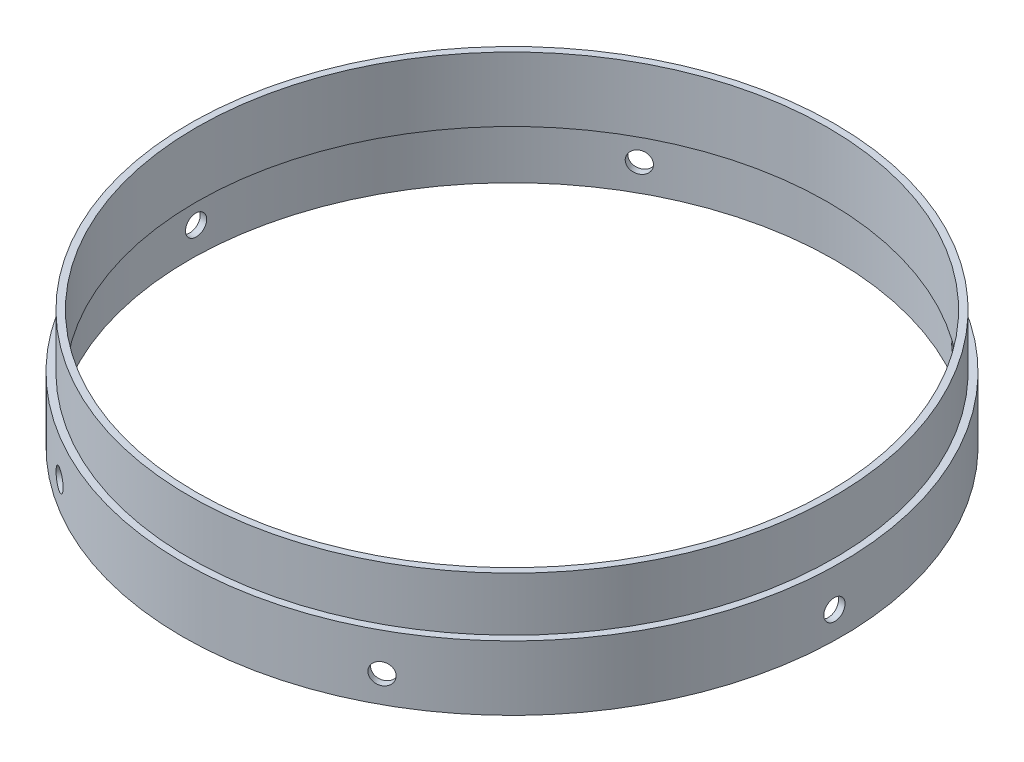
SolidWorks part; units mm, degrees
material "6061-T6 (SS)"
ref_plane "Front Plane" through (0, 0, 0) normal (0, 0, 1) x (1, 0, 0)
ref_plane "Top Plane" through (0, 0, 0) normal (0, 1, 0) x (1, 0, 0)
ref_plane "Right Plane" through (0, 0, 0) normal (1, 0, 0) x (0, 0, -1)
ref_axis "Axis1" through (0, -55, 0) along (0, 1, 0)
sketch "Sketch1" plane through (0, 0, 0) normal (0, 0, 1) x (1, 0, 0)
  line L0 (77.8637, 0) -> (77.8637, 15.24)
  line L1 (77.8637, 15.24) -> (76.2, 15.24)
  line L2 (76.2, 15.24) -> (76.2, 27.94)
  line L3 (76.2, 27.94) -> (74.6125, 27.94)
  line L4 (74.6125, 27.94) -> (74.6125, 12.7)
  line L5 (74.6125, 12.7) -> (76.2889, 12.7)
  line L6 (76.2889, 12.7) -> (76.2889, 0)
  line L7 (76.2889, 0) -> (77.8637, 0)
  line L8 (0, -55) -> (0, 55) construction
  line L9 (55, 0) -> (-55, 0) construction
  dimension "D1" = 77.8637
  dimension "D2" = 76.2889
  dimension "D3" = 76.2
  dimension "D4" = 2.54
  dimension "D5" = 74.6125
  dimension "D6" = 12.7
  dimension "D7" = 12.7
revolve "Revolve1" add sketch "Sketch1" angle 360 about axis through (0, -55, 0) along (0, 1, 0)
hole_wizard "#10 (0.1935) Diameter Hole1" positions "3DSketch1" profile "Sketch2" hole size "#10" standard "ANSI Inch"
sketch3d "3DSketch1"
  point P0 (37.5084, 6.35, 68.234)
  dimension "D1" = 6.35
sketch "Sketch2" plane through (37.5084, 6.35, 68.234) normal (0, 1, 0) x (0.8763, 0, -0.4817)
  line L0 (0, 0) -> (0, 182.6406)
  line L1 (0, 182.6406) -> (2.4574, 182.6406)
  line L2 (2.4574, 182.6406) -> (2.4574, 0)
  line L5 (2.4574, 0) -> (0, 0)
  line L11 (0, -6.35) -> (0, 107.95) construction
  dimension "Thru Hole Dia." = 4.9149
  dimension "Thru Hole Depth" = 182.6406
pattern_circular "CirPattern1" count 6 over 360 about axis through (0, -55, 0) along (0, 1, 0) of "#10 (0.1935) Diameter Hole1"
